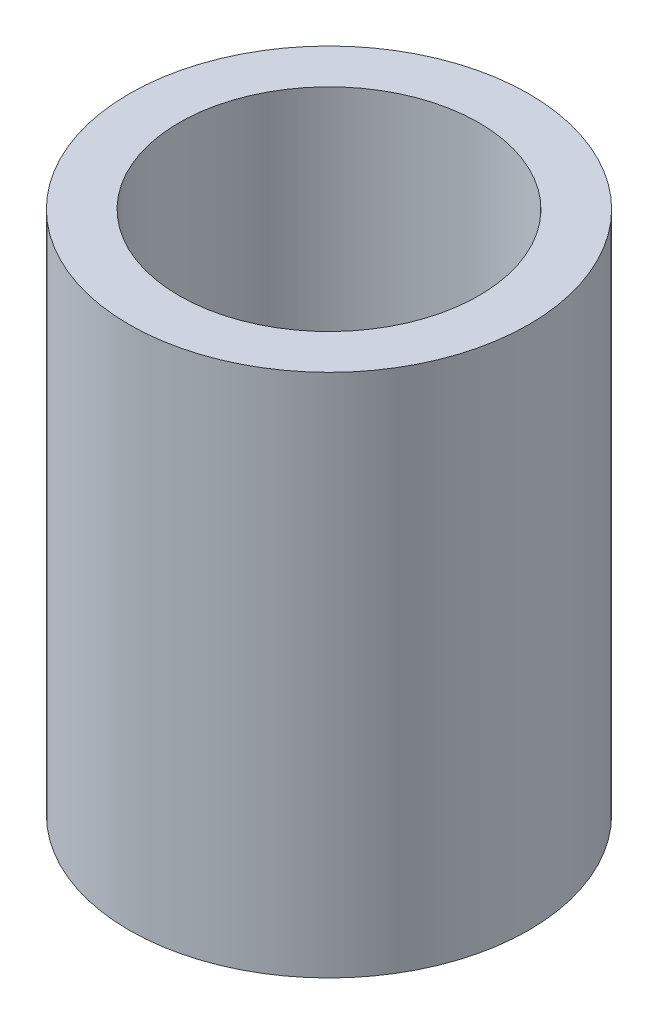
SolidWorks part; units mm, degrees
material "Ceramic Porcelain"
ref_plane "Front Plane" through (0, 0, 0) normal (0, 0, 1) x (1, 0, 0)
ref_plane "Top Plane" through (0, 0, 0) normal (0, 1, 0) x (1, 0, 0)
ref_plane "Right Plane" through (0, 0, 0) normal (1, 0, 0) x (0, 0, -1)
sketch "Sketch1" plane through (0, 0, 0) normal (0, 0, 1) x (1, 0, 0)
  line L0 (-24, 0) -> (-24, 83.984)
  line L1 (-24, 83.984) -> (-32, 83.984)
  line L2 (-32, 83.984) -> (-32, 0)
  line L3 (-32, 0) -> (-24, 0)
  line L4 (0, 0) -> (0, 31.7357)
  dimension "D1" = 24
  dimension "D2" = 8
  dimension "D3" = 83.984
revolve "Revolve1" add sketch "Sketch1" angle 360 about L4
equation "\"r_cc_inner\"= 10'combustion chamber inner radius [mm]"
equation "\"r_cc_outer\"= 24'combustion chamber outer radius [mm]"
equation "\"L_star\"= 1500'combustion process characteristic length [mm]"
equation "\"At\"= 0.0000598 * ( 1000 ) ^ 2'Throat Area [mm^2]"
equation "\"x_cc\"= \"L_star\" * \"At\" / ( pi * ( \"r_cc_outer\" ^ 2 - \"r_cc_inner\" ^ 2 ) )'combustion chamber physical length [mm]"
equation "\"x_convergent\"= 20'length of the convergent section of the nozzle [mm]"
equation "\"r_throat\"= 15'outer radius of throat gap [mm]"
equation "\"x_material_change\"= 1.5 * \"r_throat\"'distance below throat at which nozzle material changes to a low-temp material [mm]"
equation "\"t_i\"= 8'insulation thickness required by thermal considerations [mm]"
equation "\"t_cw\"= 4'pressure vessle cylinder wall thickness required by structural considerations [mm]"
equation "\"t_p\" = 1 / 4 * 25.4'pressure vessle plate thickness required by structural considerations [mm]"
equation "\"r_outer\"= \"r_cc_outer\" + \"t_i\" + \"t_cw\" + 10'overall outermost radius of engine [mm]"
equation "\"r_rod\"= 1 / 8 * 25.4 / 2'radius of the threaded rod in the center fo the spike [mm]"
equation "\"D1@Sketch1\"=\"r_cc_outer\""
equation "\"D2@Sketch1\"=\"t_i\""
equation "\"D3@Sketch1\"= \"t_i\"/2 + \"x_convergent\" + \"x_cc\""
